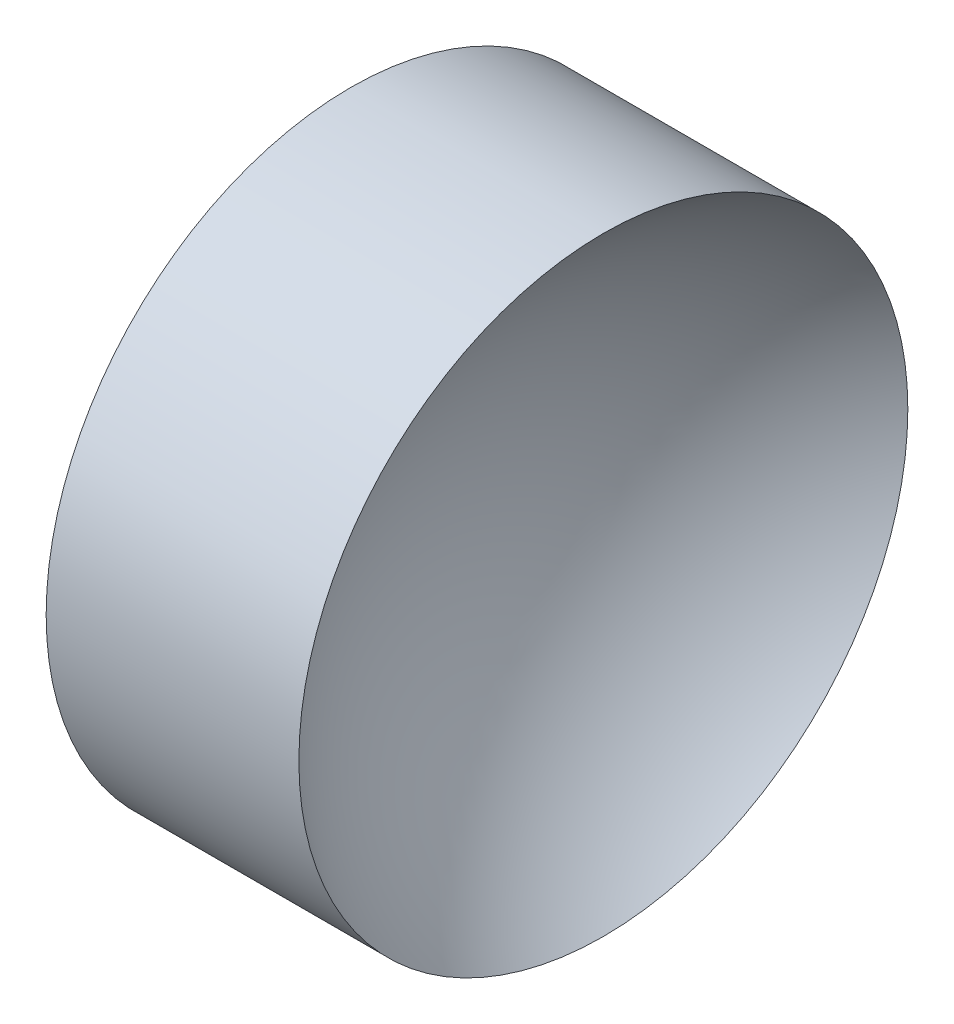
SolidWorks part; units mm, degrees
ref_plane "前视基准面" through (0, 0, 0) normal (0, 0, 1) x (1, 0, 0)
ref_plane "上视基准面" through (0, 0, 0) normal (0, 1, 0) x (1, 0, 0)
ref_plane "右视基准面" through (0, 0, 0) normal (1, 0, 0) x (0, 0, -1)
sketch "草图1" plane through (0, 0, 0) normal (0, 0, 1) x (1, 0, 0)
  line L0 (44.7821, 28.4776) -> (55.1344, 28.4776) construction
  line L1 (47.7447, 28.4776) -> (47.7447, 34.8276)
  line L2 (47.7447, 34.8276) -> (53.0151, 34.8276)
  line L3 (49.7447, 28.4776) -> (47.7447, 28.4776)
  arc A0 (53.0151, 34.8276) -> (49.7447, 28.4776) centre (57.5447, 28.4776) ccw
revolve "旋转1" add sketch "草图1" angle 360 about L0
